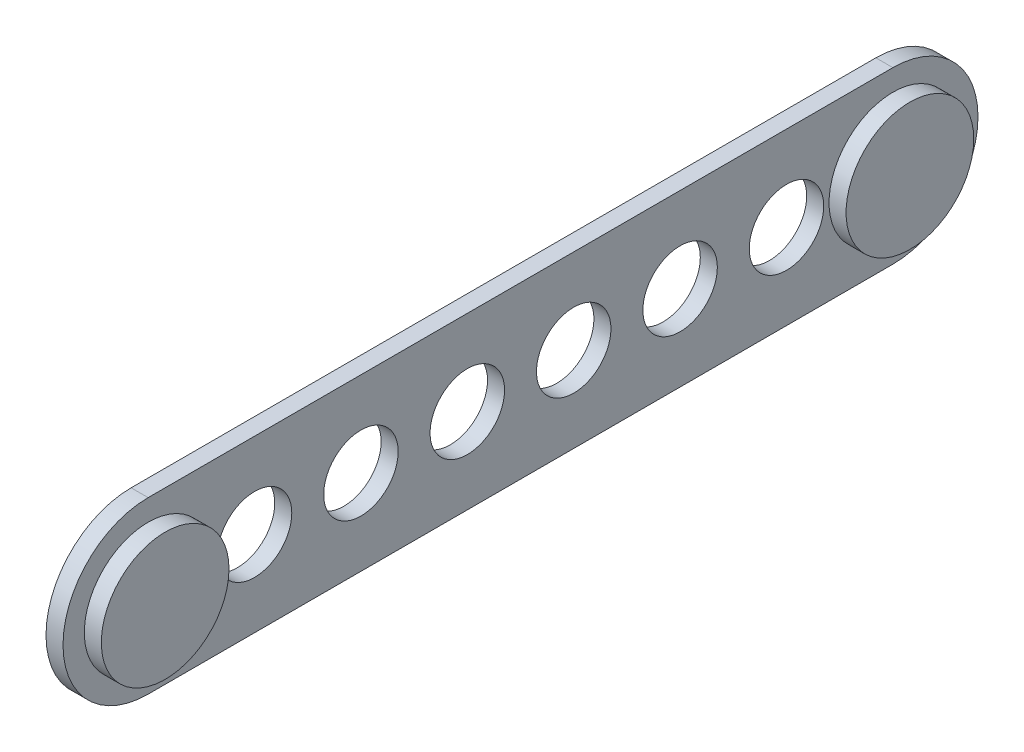
SolidWorks part; units mm, degrees
ref_plane "Front Plane" through (0, 0, 0) normal (0, 0, 1) x (1, 0, 0)
ref_plane "Top Plane" through (0, 0, 0) normal (0, 1, 0) x (1, 0, 0)
ref_plane "Right Plane" through (0, 0, 0) normal (1, 0, 0) x (0, 0, -1)
sketch "Sketch1" plane through (0, 0, 0) normal (1, 0, 0) x (0, 0, -1)
  line L0 (0, 0) -> (177.8, 0) construction
  line L1 (0, 20.32) -> (177.8, 20.32)
  line L2 (0, -20.32) -> (177.8, -20.32)
  arc A0 (0, 20.32) -> (0, -20.32) centre (0, 0) ccw
  arc A1 (177.8, -20.32) -> (177.8, 20.32) centre (177.8, 0) ccw
  point P3 (88.9, 0)
  dimension "D2" = 40.64
  dimension "D1" = 177.8
extrude "Boss-Extrude1" add sketch "Sketch1" along normal blind 4.064
sketch "Sketch2" plane through (4.064, 0, 0) normal (1, 0, 0) x (0, 0, -1)
  circle A0 centre (0, 0) radius 15.24
  circle A1 centre (177.8, 0) radius 15.24
  arc A2 (177.8, -20.32) -> (177.8, 20.32) centre (177.8, 0) ccw construction
  dimension "D1" = 30.48
  dimension "D2" = 30.48
extrude "Boss-Extrude2" add sketch "Sketch2" along normal blind 4.064
sketch "Sketch3" plane through (4.064, 0, 0) normal (1, 0, 0) x (0, 0, -1)
  circle A0 centre (25.4, 0) radius 8.89
  arc A1 (0, 20.32) -> (0, -20.32) centre (0, 0) ccw construction
  dimension "D1" = 17.78
  dimension "D2" = 25.4
extrude "Cut-Extrude1" cut sketch "Sketch3" against normal through all
pattern_linear "LPattern1" count 6 spacing 25.4 along (0, 0, -1) of "Cut-Extrude1"
